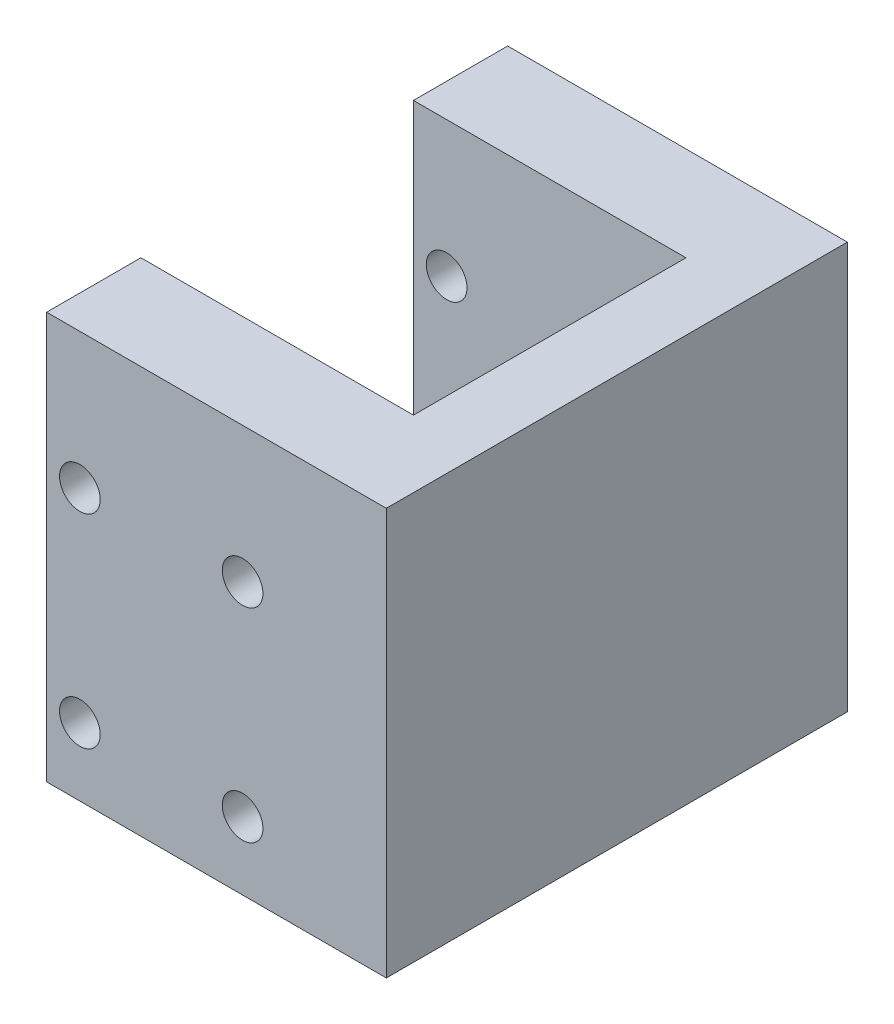
SolidWorks part; units mm, degrees
ref_plane "Front Plane" through (0, 0, 0) normal (0, 0, 1) x (1, 0, 0)
ref_plane "Top Plane" through (0, 0, 0) normal (0, 1, 0) x (1, 0, 0)
ref_plane "Right Plane" through (0, 0, 0) normal (1, 0, 0) x (0, 0, -1)
sketch "Sketch2" plane through (0, -350, 0) normal (0, -1, 0) x (1, 0, 0)
  line L1 (-398.8158, -338.6) -> (-380.3158, -338.6)
  line L3 (-398.8158, -372.6) -> (-380.3158, -372.6)
  line L7 (-378.7158, -345.55) -> (-378.7158, -365.65)
  line L12 (-373.7658, -338.6) -> (-373.7658, -372.6)
  line L16 (-398.8158, -345.55) -> (-398.8158, -365.65)
  line L17 (-398.8158, -365.65) -> (-378.7158, -365.65)
  line L18 (-378.7158, -365.65) -> (-378.7158, -345.55)
  line L19 (-378.7158, -345.55) -> (-398.8158, -345.55)
  line L22 (-373.7658, -338.6) -> (-373.7658, -372.6)
  line L25 (-398.8158, -345.55) -> (-398.8158, -365.65)
  line L28 (-398.8158, -338.6) -> (-398.8158, -345.55)
  line L29 (-398.8158, -365.65) -> (-398.8158, -372.6)
  line L30 (-380.3158, -372.6) -> (-373.7658, -372.6)
  line L31 (-380.3158, -338.6) -> (-373.7658, -338.6)
  line L32 (-398.7658, -345.6) -> (-378.7658, -345.6) construction
  line L33 (-378.7658, -345.6) -> (-378.7658, -365.6) construction
  line L34 (-378.7658, -365.6) -> (-398.7658, -365.6) construction
  line L35 (-398.7658, -365.6) -> (-398.7658, -345.6) construction
  dimension "D2" = 6.95
  dimension "D3" = 6.95
  dimension "D4" = 0.05
  dimension "D5" = 4.95
  dimension "D1" = 0.05
  dimension "D6" = 0.05
  dimension "D7" = 0.05
extrude "Extrude1" add sketch "Sketch2" against normal blind 30
sketch "Sketch3" plane through (0, 0, -338.6) normal (0, 0, 1) x (1, 0, 0)
  circle A0 centre (-384.3658, -345) radius 1.5 construction
  circle A1 centre (-396.3658, -345) radius 1.5 construction
  circle A2 centre (-384.3658, -330) radius 1.5 construction
  circle A3 centre (-396.3658, -330) radius 1.5 construction
  circle A4 centre (-384.3658, -345) radius 1.5
  circle A5 centre (-396.3658, -345) radius 1.5
  circle A6 centre (-384.3658, -330) radius 1.5
  circle A7 centre (-396.3658, -330) radius 1.5
extrude "Cut-Extrude1" cut sketch "Sketch3" against normal blind 30
